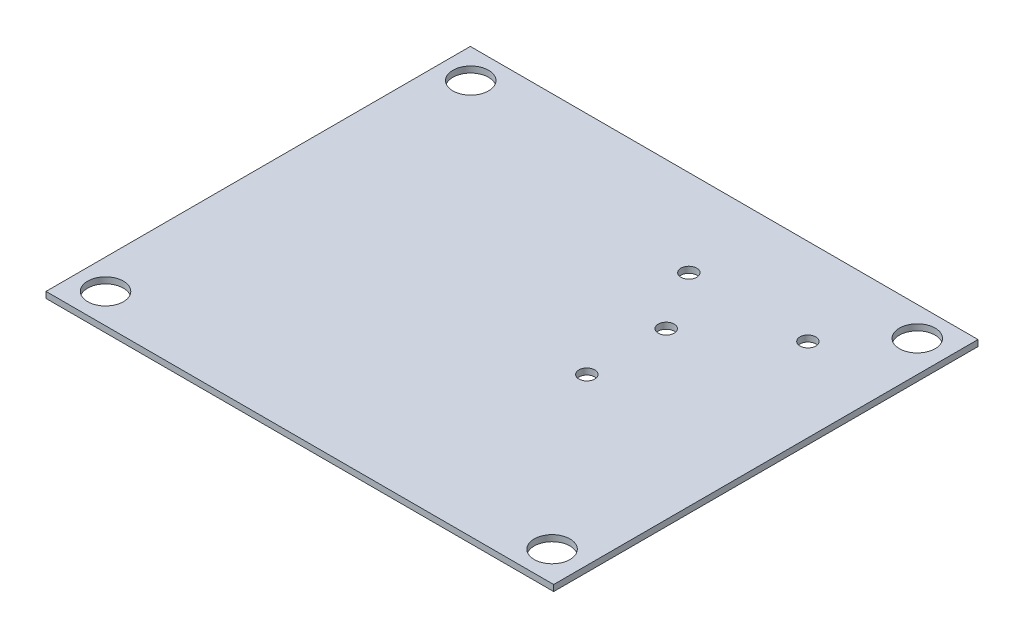
SolidWorks part; units mm, degrees
ref_plane "Front Plane" through (0, 0, 0) normal (0, 0, 1) x (1, 0, 0)
ref_plane "Top Plane" through (0, 0, 0) normal (0, 1, 0) x (1, 0, 0)
ref_plane "Right Plane" through (0, 0, 0) normal (1, 0, 0) x (0, 0, -1)
sketch "Sketch1" plane through (0, 0, 0) normal (0, 1, 0) x (1, 0, 0)
  line L1 (32.4866, -27.1526) -> (-32.4866, -27.1526)
  line L2 (32.4866, -27.1526) -> (32.4866, 27.1526)
  line L3 (32.4866, 27.1526) -> (-32.4866, 27.1526)
  line L4 (-32.4866, -27.1526) -> (-32.4866, 27.1526)
  line L5 (32.4866, -27.1526) -> (-32.4866, 27.1526) construction
  line L6 (32.4866, 27.1526) -> (-32.4866, -27.1526) construction
  circle A1 centre (-28.6766, -23.3426) radius 2.286
  circle A2 centre (28.4734, -23.3426) radius 2.286
  circle A3 centre (28.4734, 23.3934) radius 2.286
  circle A4 centre (-28.6766, 23.3934) radius 2.286
  circle A5 centre (11.3284, -1.7526) radius 1.016
  circle A6 centre (11.3284, 8.4074) radius 1.016
  circle A7 centre (6.5786, 16.0528) radius 1.016
  circle A8 centre (21.8186, 16.0528) radius 1.016
  point P0 (0, 0)
  dimension "D3" = 2
  dimension "D5" = 3.81
  dimension "D9" = 2
  dimension "D10" = 25.908
  dimension "D12" = 2
  dimension "D1" = 64.9732
  dimension "D2" = 54.3052
  dimension "D4" = 2
  dimension "D6" = 3.81
  dimension "D7" = 43.815
  dimension "D8" = 25.4
  dimension "D11" = 11.0998
extrude "Boss-Extrude1" add sketch "Sketch1" along normal blind 0.7874
